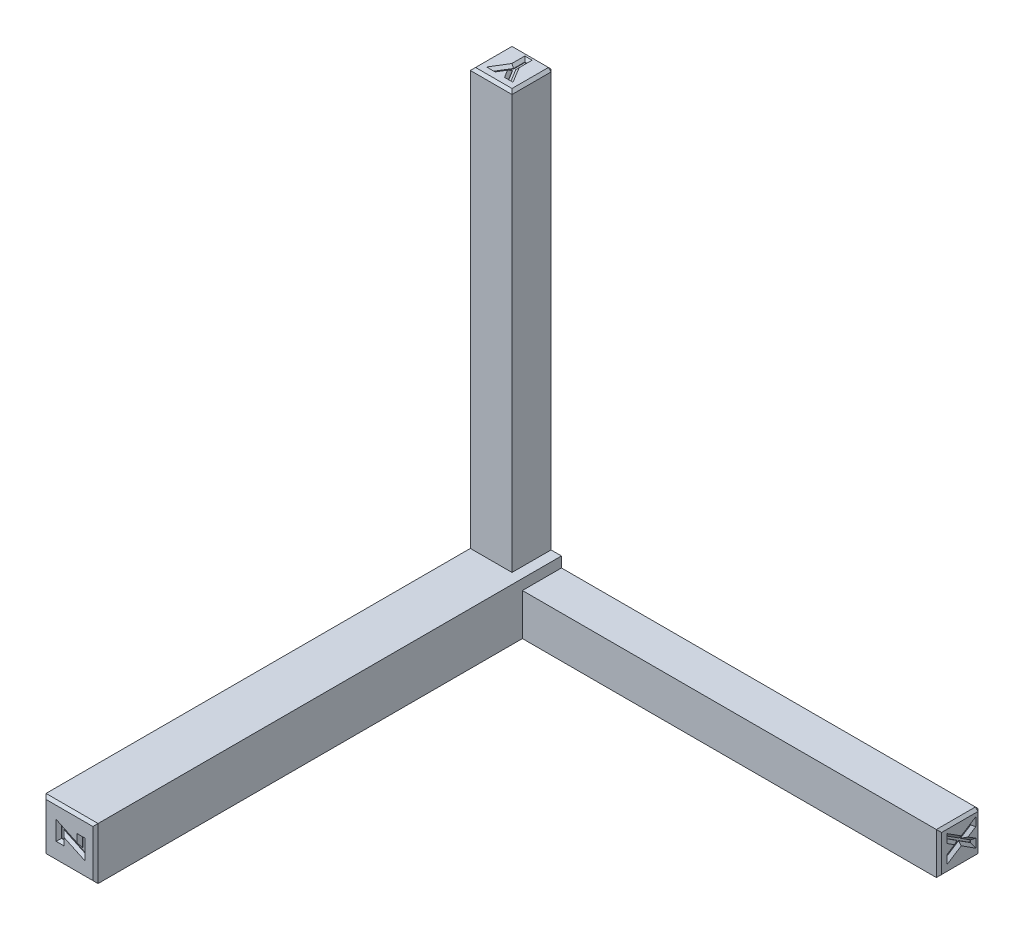
SolidWorks part; units mm, degrees
ref_plane "Front Plane" through (0, 0, 0) normal (0, 0, 1) x (1, 0, 0)
ref_plane "Top Plane" through (0, 0, 0) normal (0, 1, 0) x (1, 0, 0)
ref_plane "Right Plane" through (0, 0, 0) normal (1, 0, 0) x (0, 0, -1)
sketch "Sketch1" plane through (0, 0, 0) normal (0, 0, 1) x (1, 0, 0)
  line L1 (0, 0) -> (10, 0)
  line L2 (0, 0) -> (0, 10)
  line L3 (0, 10) -> (10, 10)
  line L4 (10, 0) -> (10, 10)
  dimension "D1" = 10
extrude "Boss-Extrude1" add sketch "Sketch1" along normal blind 90
sketch "Sketch2" plane through (10, 0, 0) normal (1, 0, 0) x (0, 0, -1)
  line L1 (0, 0) -> (-8, 0)
  line L2 (0, 0) -> (0, 8)
  line L3 (0, 8) -> (-8, 8)
  line L4 (-8, 0) -> (-8, 8)
  dimension "D1" = 8
extrude "Boss-Extrude2" add sketch "Sketch2" along normal offset from surface (80 mm away) 90 up to face at (0, 5, 45)
sketch "Sketch3" plane through (0, 10, 0) normal (0, 1, 0) x (1, 0, 0)
  line L0 (90, 0) -> (90, -8) construction
  line L1 (0, 0) -> (8, 0)
  line L2 (0, 0) -> (0, -8)
  line L3 (0, -8) -> (8, -8)
  line L4 (8, 0) -> (8, -8)
extrude "Boss-Extrude3" add sketch "Sketch3" along normal offset from surface (80 mm away) 90 up to face at (40, 0, 39.5)
sketch "Sketch6" plane through (90, 0, 0) normal (1, 0, 0) x (0, 0, -1)
  line L0 (-1.4231, 6.1234) -> (-1.4231, 2.5044) construction
  text T0 "X" font "Century Gothic" height 4.5
extrude "Cut-Extrude1" cut sketch "Sketch6" against normal blind 0.6
sketch "Sketch7" plane through (0, 90, 0) normal (0, 1, 0) x (0, 0, -1)
  line L0 (-1.3655, -1.8519) -> (-1.3655, -6.7328) construction
  text T0 "<r90>Y</r>" font "Century Gothic" height 4.5
extrude "Cut-Extrude2" cut sketch "Sketch7" against normal blind 0.6
sketch "Sketch8" plane through (0, 0, 90) normal (0, 0, 1) x (1, 0, 0)
  line L0 (7.4606, 6.653) -> (7.4606, 2.5924) construction
  text T0 "<r0>Z</r>" font "Century Gothic" height 4.5
extrude "Cut-Extrude3" cut sketch "Sketch8" against normal blind 0.6
chamfer "Chamfer1" distance 0.5 angle 45 47 edges at (5.4413, 4.7699, 90) (7.4606, 5.0664, 90) (7.2298, 6.3068, 90) (6.999, 5.3919, 90) (4.9798, 5.4207, 90) (2.9606, 5.1818, 90) (3.1913, 3.9991, 90) (3.4221, 4.8564, 90) (5, 10, 90) (10, 5, 90) (5, 0, 90) (0, 5, 90) (4.0263, 90, 1.3655) (3.8243, 90, 2.435) (3.1032, 90, 4.685) (2.6132, 90, 5.8655) (3.4349, 90, 4.8987) (4.6167, 90, 4.8987) (5.4393, 90, 5.8655) (4.9493, 90, 4.685) (4.2282, 90, 2.435) (90, 5.6307, 5.9231) (90, 4.8086, 5.0027) (90, 3.6304, 5.0027) (90, 2.8083, 5.9231) (90, 3.2807, 4.8206) (90, 3.2518, 2.5706) (90, 2.7506, 1.4231) (90, 3.6016, 2.3885) (90, 4.8375, 2.3885) (90, 5.6884, 1.4231) (90, 5.1868, 2.5706) (90, 5.1579, 4.8206) (8, 90, 4) (4, 90, 8) (0, 90, 4) (90, 4, 8) (90, 8, 4) (90, 0, 4) (45, 0, 0) (90, 4, 0) (4, 90, 0) (0, 45, 0)
